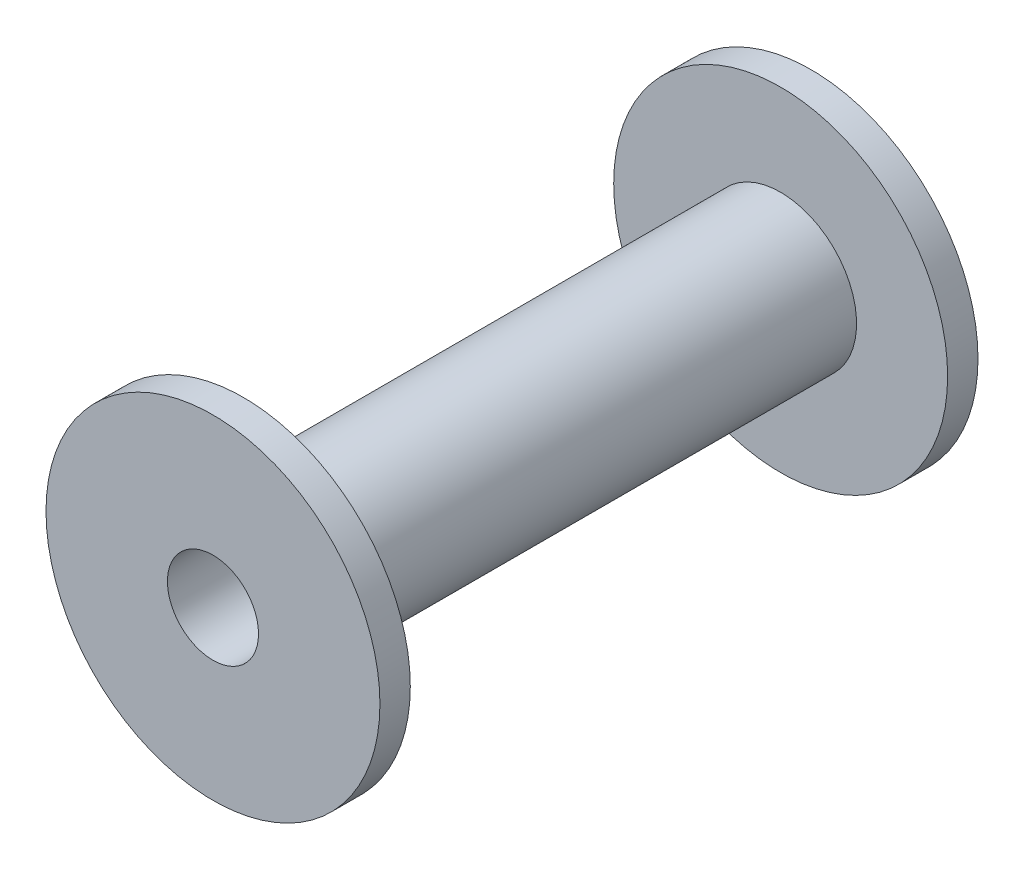
SolidWorks part; units mm, degrees
ref_plane "Plan de face" through (0, 0, 0) normal (0, 0, 1) x (1, 0, 0)
ref_plane "Plan de dessus" through (0, 0, 0) normal (0, 1, 0) x (1, 0, 0)
ref_plane "Plan de droite" through (0, 0, 0) normal (1, 0, 0) x (0, 0, -1)
sketch "Esquisse1" plane through (0, 0, 0) normal (0, 0, 1) x (1, 0, 0)
  circle A0 centre (0, 0) radius 1.5
  circle A1 centre (0, 0) radius 2.5
  dimension "D1" = 3
  dimension "D2" = 1
extrude "Boss.-Extru.1" add sketch "Esquisse1" along normal blind 9.85
sketch "Esquisse2" plane through (0, 0, 9.85) normal (0, 0, 1) x (1, 0, 0)
  circle A1 centre (0, 0) radius 2.5
  circle A2 centre (0, 0) radius 2.5 construction
  circle A3 centre (0, 0) radius 5.5
  dimension "D1" = 3
extrude "Boss.-Extru.2" add sketch "Esquisse2" against normal blind 1
mirror "Symétrie1" about plane through (0, 0, 0) normal (0, 0, 1) of "Boss.-Extru.2", "Boss.-Extru.1"
